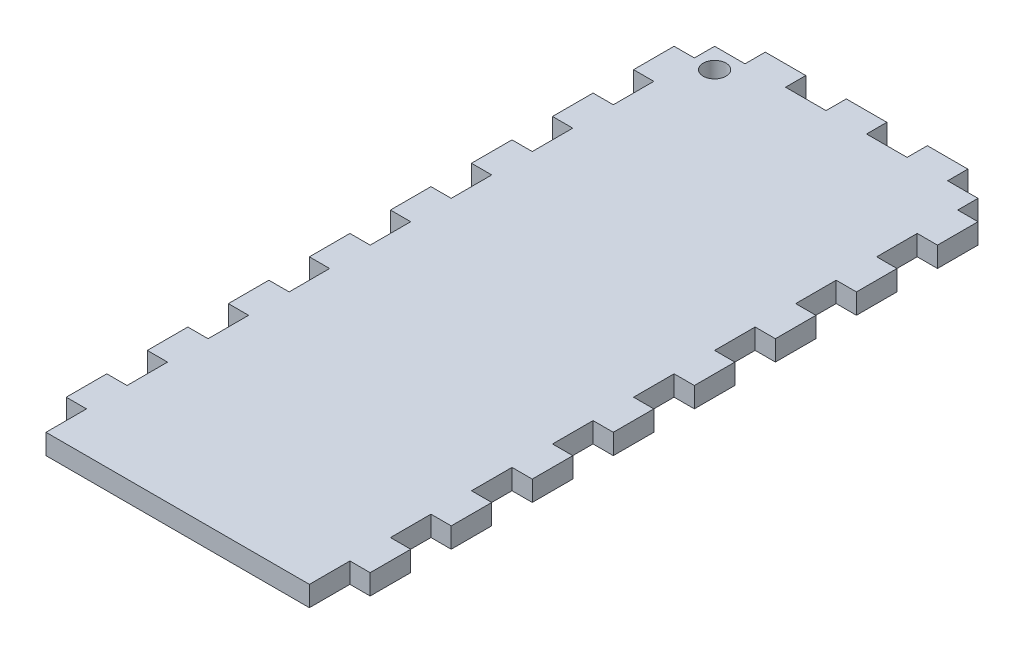
SolidWorks part; units mm, degrees
material "Pine"
ref_plane "Front Plane" through (0, 0, 0) normal (0, 0, 1) x (1, 0, 0)
ref_plane "Top Plane" through (0, 0, 0) normal (0, 1, 0) x (1, 0, 0)
ref_plane "Right Plane" through (0, 0, 0) normal (1, 0, 0) x (0, 0, -1)
sketch "Sketch1" plane through (0, 0, 0) normal (0, 1, 0) x (1, 0, 0)
  line L1 (0, 0) -> (95.25, 0)
  line L2 (0, 0) -> (0, 215.9)
  line L3 (0, 215.9) -> (95.25, 215.9)
  line L4 (95.25, 0) -> (95.25, 215.9)
  dimension "D1" = 95.25
  dimension "D2" = 215.9
extrude "Boss-Extrude1" add sketch "Sketch1" along normal blind 6.35
sketch "Sketch2" plane through (0, 6.35, 0) normal (0, 1, 0) x (1, 0, 0)
  line L0 (0, 215.9) -> (0, 0) construction
  line L1 (0, 203.2) -> (6.35, 203.2)
  line L2 (0, 203.2) -> (0, 215.9)
  line L3 (0, 215.9) -> (6.35, 215.9)
  line L4 (6.35, 203.2) -> (6.35, 215.9)
  line L5 (95.25, 215.9) -> (0, 215.9) construction
  line L6 (95.25, 0) -> (95.25, 215.9) construction
  line L7 (88.9, 215.9) -> (95.25, 215.9)
  line L8 (88.9, 215.9) -> (88.9, 203.2)
  line L9 (88.9, 203.2) -> (95.25, 203.2)
  line L10 (95.25, 215.9) -> (95.25, 203.2)
  dimension "D1" = 6.35
  dimension "D2" = 12.7
extrude "Cut-Extrude1" cut sketch "Sketch2" against normal through all
pattern_linear "LPattern1" count 10 spacing 25.4 along (0, 0, 1) of "Cut-Extrude1"
sketch "Sketch3" plane through (0, 6.35, 0) normal (0, 1, 0) x (1, 0, 0)
  line L0 (88.9, 215.9) -> (6.35, 215.9) construction
  line L1 (28.575, 215.9) -> (41.275, 215.9)
  line L2 (28.575, 215.9) -> (28.575, 209.55)
  line L3 (28.575, 209.55) -> (41.275, 209.55)
  line L4 (41.275, 215.9) -> (41.275, 209.55)
  point P6 (47.625, 215.9)
  dimension "D1" = 6.35
  dimension "D2" = 6.35
  dimension "D3" = 12.7
extrude "Cut-Extrude2" cut sketch "Sketch3" against normal through all
pattern_linear "LPattern2" count 2 spacing 25.4 along (-1, 0, 0) count 3 spacing 25.4 along (1, 0, 0) of "Cut-Extrude2"
sketch "Sketch4" plane through (0, 6.35, 0) normal (0, 1, 0) x (1, 0, 0)
  line L0 (6.35, 209.55) -> (15.875, 209.55) construction
  line L1 (6.35, 203.2) -> (6.35, 209.55) construction
  circle A0 centre (12.7, 203.2) radius 3.5719
  dimension "D1" = 7.1437
  dimension "D2" = 6.35
  dimension "D3" = 6.35
extrude "Cut-Extrude3" cut sketch "Sketch4" against normal through all
